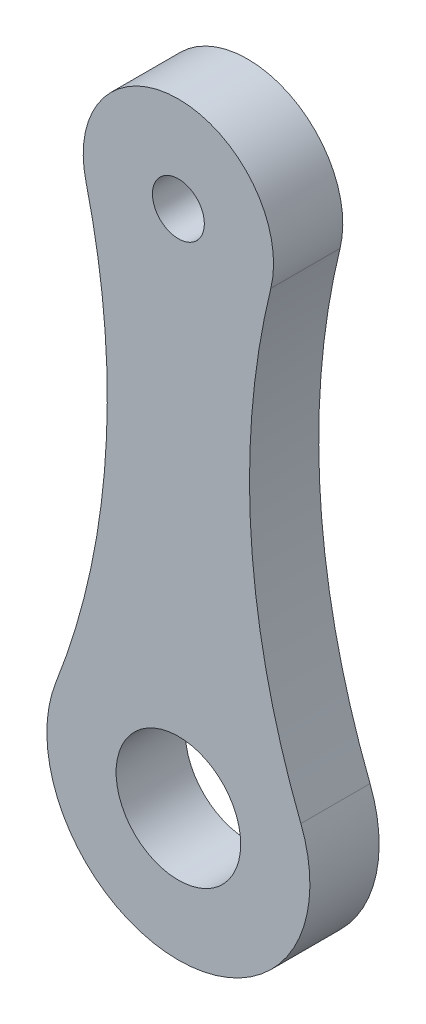
SolidWorks part; units mm, degrees
ref_plane "Front Plane" through (0, 0, 0) normal (0, 0, 1) x (1, 0, 0)
ref_plane "Top Plane" through (0, 0, 0) normal (0, 1, 0) x (1, 0, 0)
ref_plane "Right Plane" through (0, 0, 0) normal (1, 0, 0) x (0, 0, -1)
sketch "Sketch1" plane through (0, 0, 0) normal (0, 0, 1) x (1, 0, 0)
  line L0 (0, 15) -> (0, -15) construction
  line L3 (-4.25, 0) -> (4.25, 0) construction
  circle A2 centre (0, -15) radius 3.6
  circle A3 centre (0, 15) radius 1.5
  arc A4 (-7.0759, -12.2267) -> (7.0759, -12.2267) centre (0, -15) ccw
  arc A5 (5.3424, 13.6928) -> (-5.3424, 13.6928) centre (0, 15) ccw
  arc A6 (-5.3424, 13.6928) -> (-7.0759, -12.2267) centre (-47.1242, 3.4695) cw
  arc A7 (5.3424, 13.6928) -> (7.0759, -12.2267) centre (47.1242, 3.4695) ccw
  point P3 (0, 0)
  point P16 (0, 0)
  dimension "D1" = 3
  dimension "D2" = 7.2
  dimension "D3" = 4
  dimension "D6" = 8.5
  dimension "D5" = 30
  dimension "D4" = 4
extrude "Boss-Extrude1" add sketch "Sketch1" along normal blind 4 contours A7 A5 A6 A4 A3 A2
